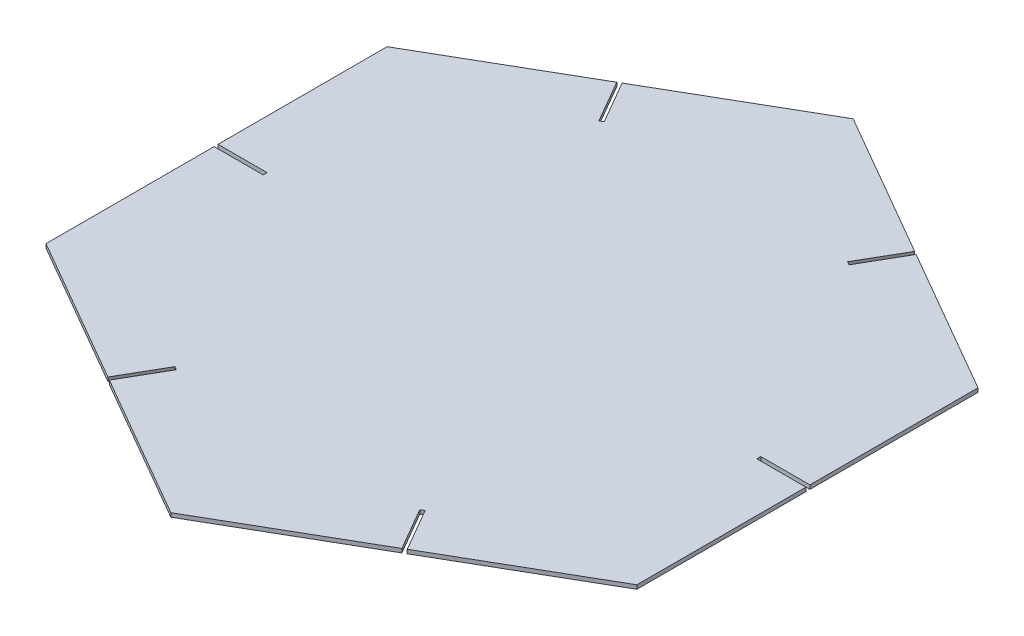
SolidWorks part; units mm, degrees
ref_plane "Front Plane" through (0, 0, 0) normal (0, 0, 1) x (1, 0, 0)
ref_plane "Top Plane" through (0, 0, 0) normal (0, 1, 0) x (1, 0, 0)
ref_plane "Right Plane" through (0, 0, 0) normal (1, 0, 0) x (0, 0, -1)
sketch "Sketch2" plane through (0, 0, 0) normal (0, 1, 0) x (1, 0, 0)
  line L1 (0, 69.5079) -> (-60.1956, 34.7539)
  line L2 (-60.1956, 34.7539) -> (-60.1956, -34.7539)
  line L3 (-60.1956, -34.7539) -> (0, -69.5079)
  line L4 (0, -69.5079) -> (60.1956, -34.7539)
  line L5 (60.1956, -34.7539) -> (60.1956, 34.7539)
  line L6 (60.1956, 34.7539) -> (0, 69.5079)
  circle A0 centre (0, 0) radius 60.1956 construction
extrude "Boss-Extrude1" add sketch "Sketch2" along normal blind 0.8
sketch "Sketch3" plane through (0, 0, 0) normal (0, -1, 0) x (1, 0, 0)
  line L0 (60.1956, 34.7539) -> (60.1956, -34.7539) construction
  line L5 (60.1956, 0) -> (-60.1956, 0) construction
  line L6 (-60.1956, -34.7539) -> (-60.1956, 34.7539) construction
  line L7 (0, -69.5079) -> (0, 69.5079) construction
  line L8 (29.6648, -52.3809) -> (24.6648, -43.7206)
  line L9 (60.1956, -0.5) -> (50.1956, -0.5)
  line L10 (60.1956, -0.5) -> (60.1956, 0.3)
  line L11 (60.1956, 0.3) -> (50.1956, 0.3)
  line L12 (50.1956, -0.5) -> (50.1956, 0.3)
  line L13 (30.3576, -51.9809) -> (25.3576, -43.3206)
  line L14 (24.6648, -43.7206) -> (25.3576, -43.3206)
  line L15 (29.6648, -52.3809) -> (30.3576, -51.9809)
  line L16 (-30.5308, -51.8809) -> (-25.5308, -43.2206)
  line L17 (-29.838, -52.2809) -> (-24.838, -43.6206)
  line L18 (-25.5308, -43.2206) -> (-24.838, -43.6206)
  line L19 (-30.5308, -51.8809) -> (-29.838, -52.2809)
  line L20 (-60.1956, 0.5) -> (-50.1956, 0.5)
  line L21 (-60.1956, -0.3) -> (-50.1956, -0.3)
  line L22 (-50.1956, 0.5) -> (-50.1956, -0.3)
  line L23 (-60.1956, 0.5) -> (-60.1956, -0.3)
  line L24 (-29.6648, 52.3809) -> (-24.6648, 43.7206)
  line L25 (-30.3576, 51.9809) -> (-25.3576, 43.3206)
  line L26 (-24.6648, 43.7206) -> (-25.3576, 43.3206)
  line L27 (-29.6648, 52.3809) -> (-30.3576, 51.9809)
  line L28 (30.5308, 51.8809) -> (25.5308, 43.2206)
  line L29 (29.838, 52.2809) -> (24.838, 43.6206)
  line L30 (25.5308, 43.2206) -> (24.838, 43.6206)
  line L31 (30.5308, 51.8809) -> (29.838, 52.2809)
  dimension "D1" = 10
  dimension "D2" = 0.8
  dimension "D3" = 0.5
  dimension "D4" = 6
extrude "Cut-Extrude1" cut sketch "Sketch3" against normal through all
